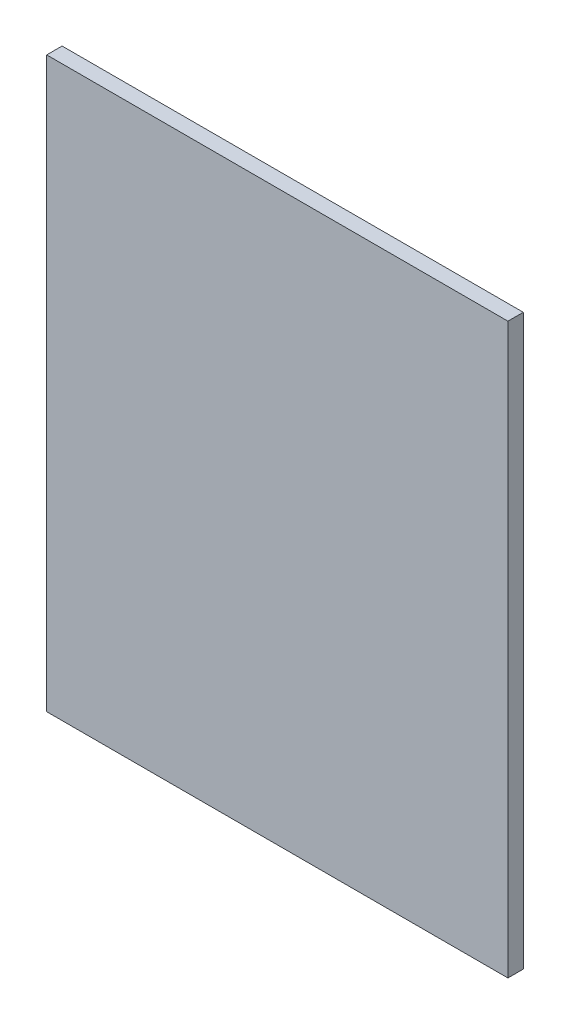
SolidWorks part; units mm, degrees
ref_plane "前视基准面" through (0, 0, 0) normal (0, 0, 1) x (1, 0, 0)
ref_plane "上视基准面" through (0, 0, 0) normal (0, 1, 0) x (1, 0, 0)
ref_plane "右视基准面" through (0, 0, 0) normal (1, 0, 0) x (0, 0, -1)
sketch "草图1" plane through (0, 0, 0) normal (0, 0, 1) x (1, 0, 0)
  line L0 (-48.4462, 33.5396) -> (251.5538, 33.5396)
  line L1 (251.5538, 33.5396) -> (251.5538, -336.4604)
  line L2 (251.5538, -336.4604) -> (-48.4462, -336.4604)
  line L3 (-48.4462, -336.4604) -> (-48.4462, 33.5396)
extrude "凸台-拉伸1" add sketch "草图1" along normal blind 10
